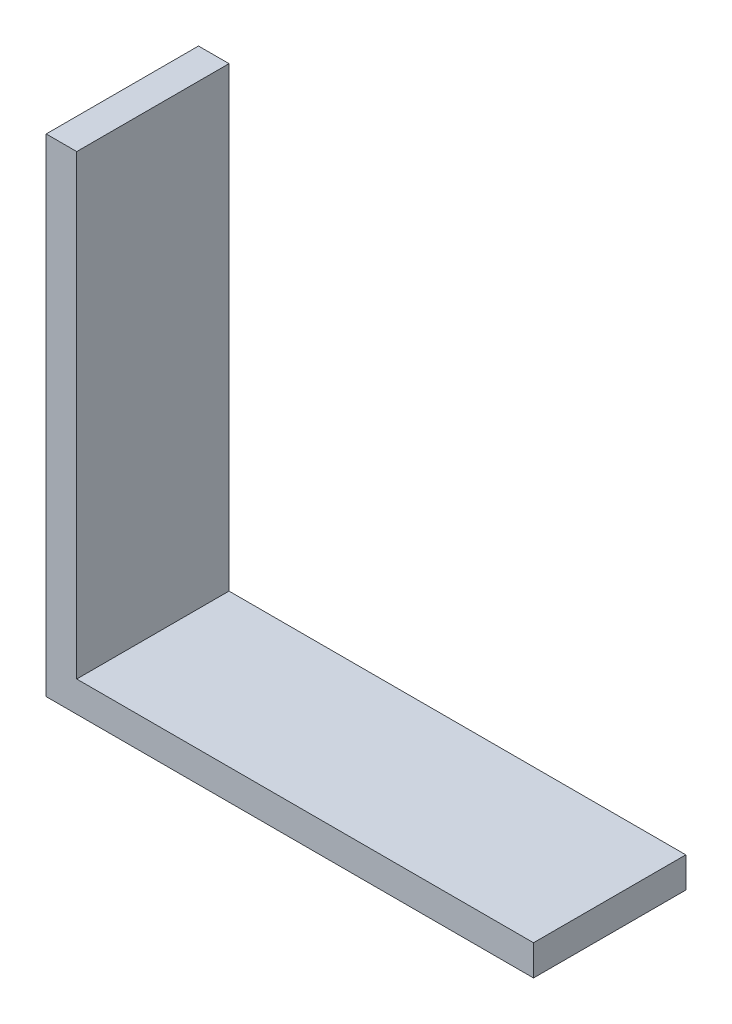
SolidWorks part; units mm, degrees
material "6063-T6"
ref_plane "Front Plane" through (0, 0, 0) normal (0, 0, 1) x (1, 0, 0)
ref_plane "Top Plane" through (0, 0, 0) normal (0, 1, 0) x (1, 0, 0)
ref_plane "Right Plane" through (0, 0, 0) normal (1, 0, 0) x (0, 0, -1)
sketch "Sketch1" plane through (0, 0, 0) normal (0, 0, 1) x (1, 0, 0)
  line L0 (0, 0) -> (0, 76.2)
  line L1 (0, 0) -> (76.2, 0)
  line L2 (0, 76.2) -> (4.7752, 76.2)
  line L3 (4.7752, 76.2) -> (4.7752, 4.7752)
  line L4 (4.7752, 4.7752) -> (76.2, 4.7752)
  line L5 (76.2, 4.7752) -> (76.2, 0)
  dimension "D1" = 76.2
  dimension "D2" = 4.7752
extrude "Boss-Extrude1" add sketch "Sketch1" along normal mid plane 23.8125
